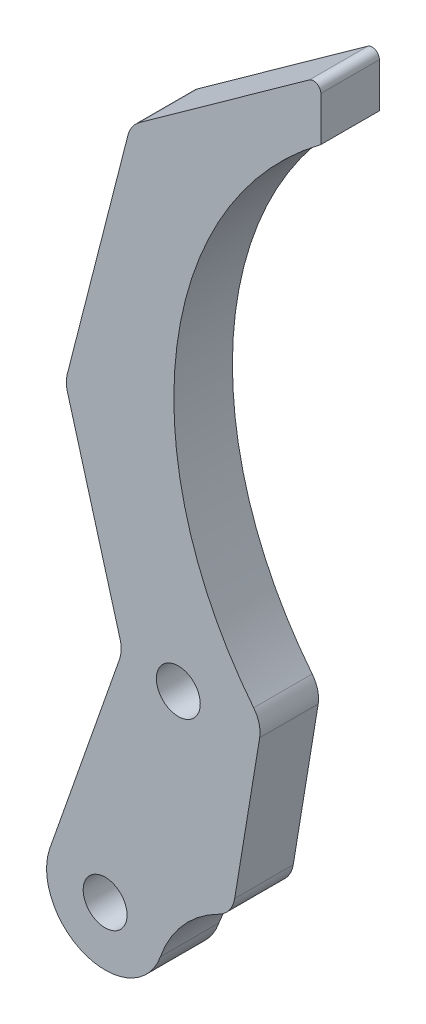
SolidWorks part; units mm, degrees
ref_plane "前视基准面" through (0, 0, 0) normal (0, 0, 1) x (1, 0, 0)
ref_plane "上视基准面" through (0, 0, 0) normal (0, 1, 0) x (1, 0, 0)
ref_plane "右视基准面" through (0, 0, 0) normal (1, 0, 0) x (0, 0, -1)
sketch "草图1" plane through (0, 0, 0) normal (0, 0, 1) x (1, 0, 0)
  line L1 (-44.759, 0) -> (37.6123, 0) construction
  line L2 (0, 0) -> (0, 68.6572) construction
  line L3 (23.6847, 21.3009) -> (7.0185, 2.6666) construction
  line L4 (29.6477, 15.9677) -> (12.9815, -2.6666) construction
  line L5 (30.4405, 19.9591) -> (22.8919, 17.3096) construction
  line L6 (16.1103, 33.6542) -> (17.8145, 23.2934) construction
  line L8 (30.4405, 19.9591) -> (25.6815, 33.5175) construction
  line L9 (25.6428, 34.7197) -> (29.2417, 47.5584) construction
  line L10 (29.2536, 48.5936) -> (25.1082, 64.8082) construction
  line L11 (19.8028, 35.3009) -> (3.1366, 16.6666) construction
  line L12 (23.5296, 31.9677) -> (6.8634, 13.3334) construction
  line L13 (24.3365, 65.9378) -> (12.7194, 74.273) construction
  line L14 (11.9279, 73.8667) -> (11.9279, 70.8409) construction
  line L15 (-23.6847, 21.3009) -> (-7.0185, 2.6666) construction
  line L16 (-29.6477, 15.9677) -> (-12.9815, -2.6666) construction
  line L17 (-23.5296, 31.9677) -> (-6.8634, 13.3334) construction
  line L18 (-19.8028, 35.3009) -> (-3.1366, 16.6666) construction
  line L19 (-16.1103, 33.6542) -> (-17.8145, 23.2934)
  line L20 (-30.4405, 19.9591) -> (-25.6815, 33.5175)
  line L25 (-25.6428, 34.7197) -> (-29.2417, 47.5584)
  line L26 (-5, 15) -> (-10, 0) construction
  line L27 (5, 15) -> (10, 0) construction
  line L28 (21.6662, 33.6343) -> (26.6662, 18.6343) construction
  line L29 (-29.2536, 48.5936) -> (-25.1082, 64.8082)
  line L30 (-24.3365, 65.9378) -> (-12.7194, 74.273)
  line L31 (-11.9279, 73.8667) -> (-11.9279, 70.8409)
  line L32 (-3.0291, 50.8087) -> (14.3488, 56.1034) construction
  circle A0 centre (-10, 0) radius 10 construction
  circle A4 centre (0, 51.7316) radius 15 construction
  circle A5 centre (10, 0) radius 4 construction
  circle A6 centre (10, 0) radius 10 construction
  arc A14 (22.8919, 17.3096) -> (17.993, 22.2086) centre (15.3434, 14.6601) ccw construction
  circle A16 centre (26.6662, 18.6343) radius 1.5 construction
  circle A17 centre (26.6662, 18.6343) radius 4 construction
  circle A18 centre (5, 15) radius 2.5 construction
  arc A19 (16.5198, 35.2255) -> (11.9279, 70.8409) centre (-3.0291, 50.8087) ccw construction
  circle A20 centre (21.6662, 33.6343) radius 2.5 construction
  circle A21 centre (-10, 0) radius 4 construction
  circle A22 centre (-26.6662, 18.6343) radius 1.5
  arc A23 (-30.4405, 19.9591) -> (-22.8919, 17.3096) centre (-26.6662, 18.6343) ccw
  arc A24 (-22.8919, 17.3096) -> (-18.8991, 21.8265) centre (-15.3434, 14.6601) cw
  circle A25 centre (-21.6662, 33.6343) radius 2.5 construction
  circle A26 centre (-5, 15) radius 2.5 construction
  circle A28 centre (-21.6662, 33.6343) radius 1.5
  circle A29 centre (-5, 15) radius 1.5 construction
  circle A30 centre (5, 15) radius 1.5 construction
  circle A31 centre (21.6662, 33.6343) radius 1.5 construction
  arc A33 (-18.8991, 21.8265) -> (-17.8145, 23.2934) centre (-19.788, 23.6181) ccw
  arc A40 (12.7194, 74.273) -> (11.9279, 73.8667) centre (12.4279, 73.8667) ccw construction
  arc A41 (18.8991, 21.8265) -> (17.8145, 23.2934) centre (19.788, 23.6181) cw construction
  arc A42 (16.1103, 33.6542) -> (16.5198, 35.2255) centre (18.0838, 33.9788) cw construction
  arc A43 (-16.5198, 35.2255) -> (-11.9279, 70.8409) centre (3.0291, 50.8087) cw
  arc A44 (25.6815, 33.5175) -> (25.6428, 34.7197) centre (27.5686, 34.1799) cw construction
  arc A45 (29.2417, 47.5584) -> (29.2536, 48.5936) centre (27.316, 48.0982) ccw construction
  arc A46 (25.1082, 64.8082) -> (24.3365, 65.9378) centre (23.1706, 64.3128) ccw construction
  arc A47 (-12.7194, 74.273) -> (-11.9279, 73.8667) centre (-12.4279, 73.8667) cw
  arc A48 (-16.1103, 33.6542) -> (-16.5198, 35.2255) centre (-18.0838, 33.9788) ccw
  arc A49 (-25.6815, 33.5175) -> (-25.6428, 34.7197) centre (-27.5686, 34.1799) ccw
  arc A50 (-29.2417, 47.5584) -> (-29.2536, 48.5936) centre (-27.316, 48.0982) cw
  arc A51 (-25.1082, 64.8082) -> (-24.3365, 65.9378) centre (-23.1706, 64.3128) cw
  point P71 (-27.5959, 18.204)
  point P72 (0, 55)
  point P73 (0, 51.2304)
  point P74 (-24.3137, 20.8834)
  point P93 (11.9279, 74.8409)
  point P96 (15.9627, 34.5512)
  point P99 (25.4726, 34.1125)
  point P102 (29.3864, 48.0744)
  point P105 (24.9279, 65.5135)
  point P109 (-11.9279, 74.8409)
  point P112 (-15.9627, 34.5512)
  point P115 (-25.4726, 34.1125)
  point P118 (-17.993, 22.2086)
  point P122 (-29.3864, 48.0744)
  point P125 (-24.9279, 65.5135)
  dimension "D1" = 30
  dimension "D3" = 20
  dimension "D4" = 25
  dimension "D5" = 8
  dimension "D6" = 3
  dimension "D7" = 2
  dimension "D8" = 8
  dimension "D13" = 25
  dimension "D20" = 140
  dimension "D21" = 5
  dimension "D27" = 3
  dimension "D29" = 0.5
  dimension "D28" = 16
  dimension "D30" = 2
  dimension "D14" = 4
  dimension "D12" = 10.5
  dimension "D18" = 150
  dimension "D10" = 0.5
  dimension "D26" = 2
  dimension "D9" = 11
  dimension "D11" = 15
  dimension "D15" = 10
  dimension "D16" = 145
  dimension "D17" = 14.5
  dimension "D19" = 18
  dimension "D22" = 5
  dimension "D23" = 15
  dimension "D24" = 25
  dimension "D25" = 3.75
extrude "凸台-拉伸1" add sketch "草图1" along normal blind 4
